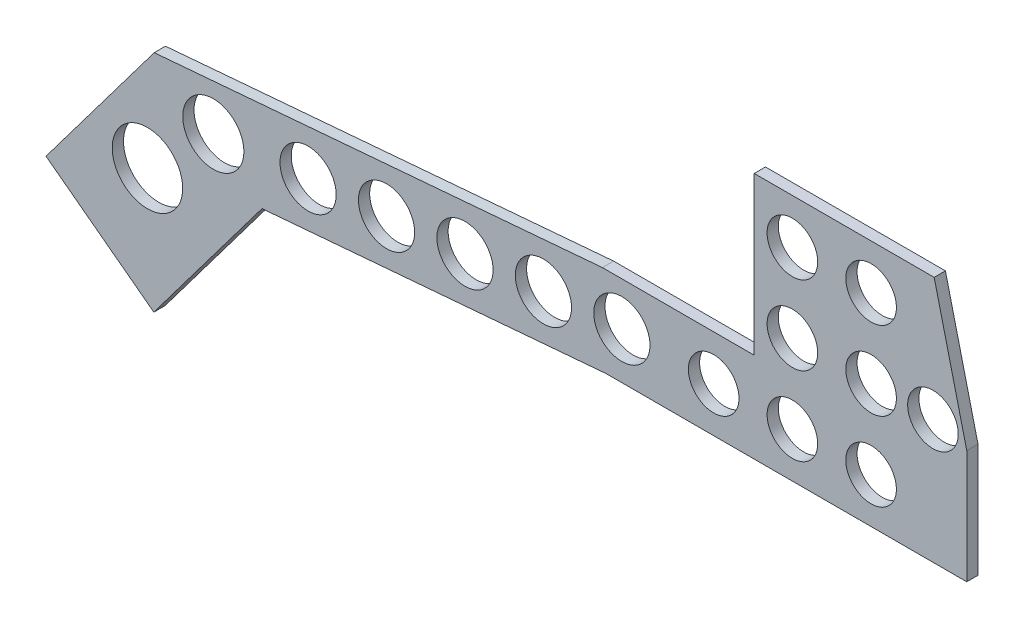
SolidWorks part; units mm, degrees
ref_plane "Front Plane" through (0, 0, 0) normal (0, 0, 1) x (1, 0, 0)
ref_plane "Top Plane" through (0, 0, 0) normal (0, 1, 0) x (1, 0, 0)
ref_plane "Right Plane" through (0, 0, 0) normal (1, 0, 0) x (0, 0, -1)
sketch "Sketch1" plane through (0, 0, 0) normal (0, 0, 1) x (1, 0, 0)
  line L0 (0, 0) -> (50.8, 0)
  line L1 (50.8, 0) -> (60, -37.7541)
  line L2 (60, -37.7541) -> (60, -69.85)
  line L3 (60, -69.85) -> (-41.7879, -69.85)
  line L4 (-41.7879, -69.85) -> (-138.9667, -78.0875)
  line L5 (-138.9667, -78.0875) -> (-169.5142, -118.6768)
  line L6 (-169.5142, -118.6768) -> (-199.9562, -95.7662)
  line L7 (-199.9562, -95.7662) -> (-169.4087, -55.1769)
  line L8 (-169.4087, -55.1769) -> (-42.8625, -44.45)
  line L9 (-42.8625, -44.45) -> (0, -44.45)
  line L10 (0, -44.45) -> (0, 0)
  dimension "D1" = 50.8
  dimension "D2" = 69.85
  dimension "D3" = 60
  dimension "D4" = 42.8625
  dimension "D5" = 44.45
  dimension "D6" = 38.1
  dimension "D7" = 50.8
  dimension "D8" = 25.4
  dimension "D9" = 50.8
  dimension "D10" = 127
extrude "Boss-Extrude1" add sketch "Sketch1" along normal blind 3.175 contours L7 L8 L9 L10 L0 L1 L2 L3 L4 L5 L6
sketch "Sketch2" plane through (0, 0, 3.175) normal (0, 0, 1) x (1, 0, 0)
  line L0 (-140.6269, -52.7372) -> (-138.4815, -78.0464) construction
  line L1 (-169.4087, -55.1769) -> (-42.8625, -44.45) construction
  line L2 (-41.7879, -69.85) -> (-138.9667, -78.0875) construction
  line L3 (-139.5542, -65.3918) -> (-34.8698, -56.518) construction
  line L4 (-21.4312, -44.45) -> (-21.4313, -69.85) construction
  line L5 (-42.8625, -44.45) -> (0, -44.45) construction
  line L6 (60, -69.85) -> (-41.7879, -69.85) construction
  circle A0 centre (-171.3148, -84.3519) radius 9.9464
  circle A1 centre (-152.715, -66.7142) radius 8.6288
  circle A2 centre (-125.9574, -64.2392) radius 7.9375
  circle A3 centre (-103.8119, -62.362) radius 7.9375
  circle A4 centre (-81.6663, -60.4848) radius 7.9375
  circle A5 centre (-59.5207, -58.6076) radius 7.9375
  circle A6 centre (-37.3751, -56.7304) radius 7.9375
  circle A7 centre (-11.4552, -57.15) radius 7.1438
  circle A8 centre (10.7698, -57.15) radius 7.1438
  circle A9 centre (32.9948, -57.15) radius 7.1437
  circle A10 centre (10.7698, -34.925) radius 7.1438
  circle A11 centre (32.9948, -34.925) radius 7.1437
  circle A12 centre (10.7698, -12.7) radius 7.1438
  circle A13 centre (32.9948, -12.7) radius 7.1437
  circle A14 centre (-11.4552, -34.925) radius 7.1438
  circle A15 centre (-11.4552, -12.7) radius 7.1438
  circle A16 centre (50.4573, -34.925) radius 7.1438
  point P14 (-21.4312, -57.15)
  dimension "D2" = 15.875
  dimension "D3" = 14.2875
  dimension "D6" = 17.4625
  dimension "D1" = 5
  dimension "D4" = 3
  dimension "D5" = 3
extrude "Cut-Extrude1" cut sketch "Sketch2" against normal through all
